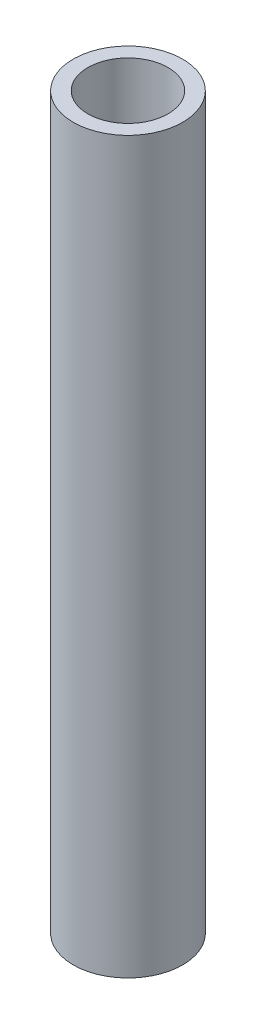
SolidWorks part; units mm, degrees
material "Brass"
ref_plane "Front Plane" through (0, 0, 0) normal (0, 0, 1) x (1, 0, 0)
ref_plane "Top Plane" through (0, 0, 0) normal (0, 1, 0) x (1, 0, 0)
ref_plane "Right Plane" through (0, 0, 0) normal (1, 0, 0) x (0, 0, -1)
sketch "Sketch1" plane through (0, 0, 0) normal (0, 1, 0) x (1, 0, 0)
  circle A0 centre (0, 0) radius 1.1
  circle A1 centre (0, 0) radius 1.5
  dimension "D1" = 2.2
  dimension "D2" = 3
extrude "Extrude1" add sketch "Sketch1" along normal blind 20
